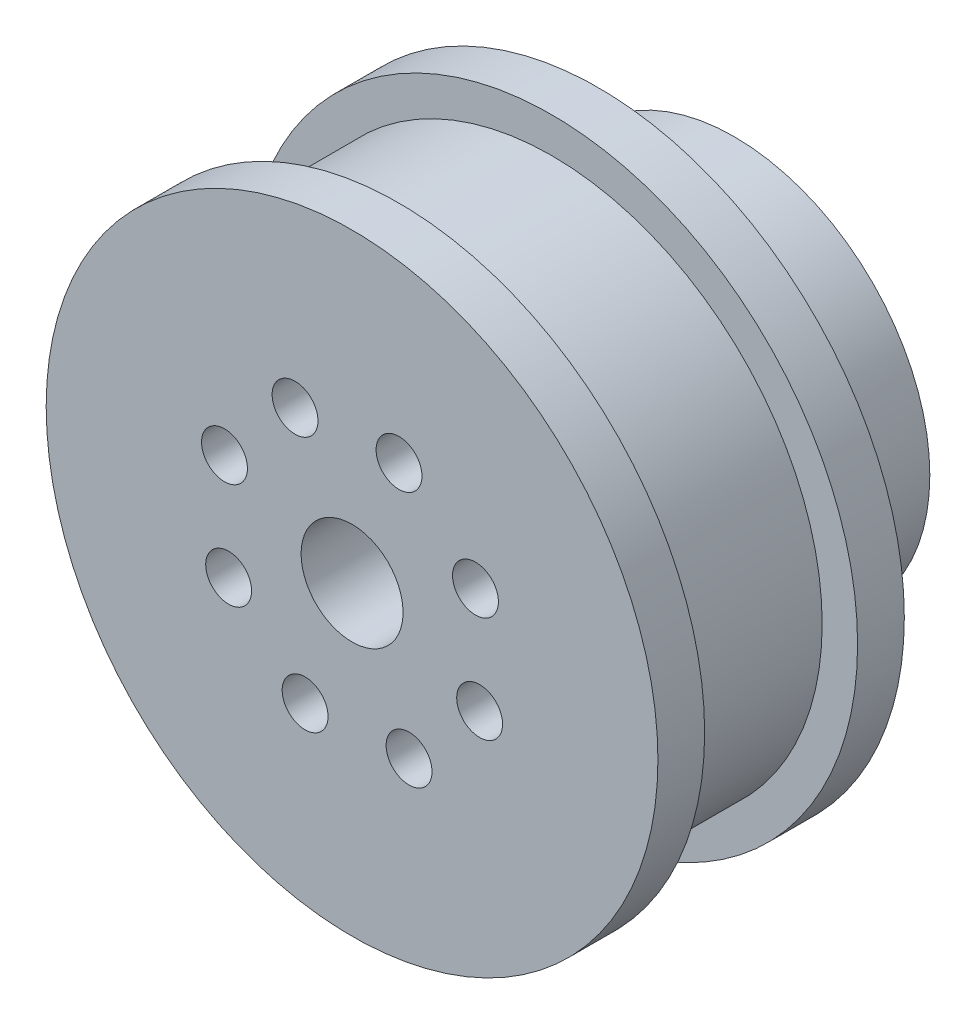
SolidWorks part; units mm, degrees
ref_plane "Plan de face" through (0, 0, 0) normal (0, 0, 1) x (1, 0, 0)
ref_plane "Plan de dessus" through (0, 0, 0) normal (0, 1, 0) x (1, 0, 0)
ref_plane "Plan de droite" through (0, 0, 0) normal (1, 0, 0) x (0, 0, -1)
sketch "Esquisse1" plane through (0, 0, 0) normal (0, 0, 1) x (1, 0, 0)
  circle A0 centre (0, 0) radius 18
  dimension "D1" = 36
extrude "Boss.-Extru.2" add sketch "Esquisse1" along normal blind 2.75
sketch "Esquisse2" plane through (0, 0, 2.75) normal (0, 0, 1) x (1, 0, 0)
  circle A0 centre (0, 0) radius 15.915
  dimension "D1" = 31.83
extrude "Boss.-Extru.3" add sketch "Esquisse2" along normal blind 9
sketch "Esquisse3" plane through (0, 0, 11.75) normal (0, 0, 1) x (1, 0, 0)
  circle A0 centre (0, 0) radius 18
  dimension "D1" = 36
extrude "Boss.-Extru.4" add sketch "Esquisse3" along normal blind 2.75
sketch "Esquisse4" plane through (0, 0, 0) normal (0, 0, -1) x (-1, 0, 0)
  circle A0 centre (0, 0) radius 11.5
  dimension "D1" = 23
extrude "Boss.-Extru.5" add sketch "Esquisse4" along normal blind 8
sketch "Esquisse5" plane through (0, 0, -8) normal (0, 0, -1) x (-1, 0, 0)
  circle A0 centre (0, 0) radius 3
  dimension "D1" = 6
extrude "Enlèv. mat.-Extru.1" cut sketch "Esquisse5" against normal through all
sketch "Esquisse6" plane through (0, 0, -8) normal (0, 0, -1) x (-1, 0, 0)
  circle A2 centre (0, 0) radius 4
  dimension "D1" = 8
extrude "Enlèv. mat.-Extru.2" cut sketch "Esquisse6" against normal blind 10
sketch "Esquisse7" plane through (0, 0, -8) normal (0, 0, -1) x (-1, 0, 0)
  circle A0 centre (3.3545, 7.2627) radius 1.35
  circle A1 centre (0, 0) radius 4 construction
  dimension "D2" = 2.7
  dimension "D1" = 8
extrude "Enlèv. mat.-Extru.3" cut sketch "Esquisse7" against normal through all
pattern_circular "Répétition circulaire1" count 8 every 45 about axis through (0, 0, 0) along (0, 0, 1) of "Enlèv. mat.-Extru.3"
